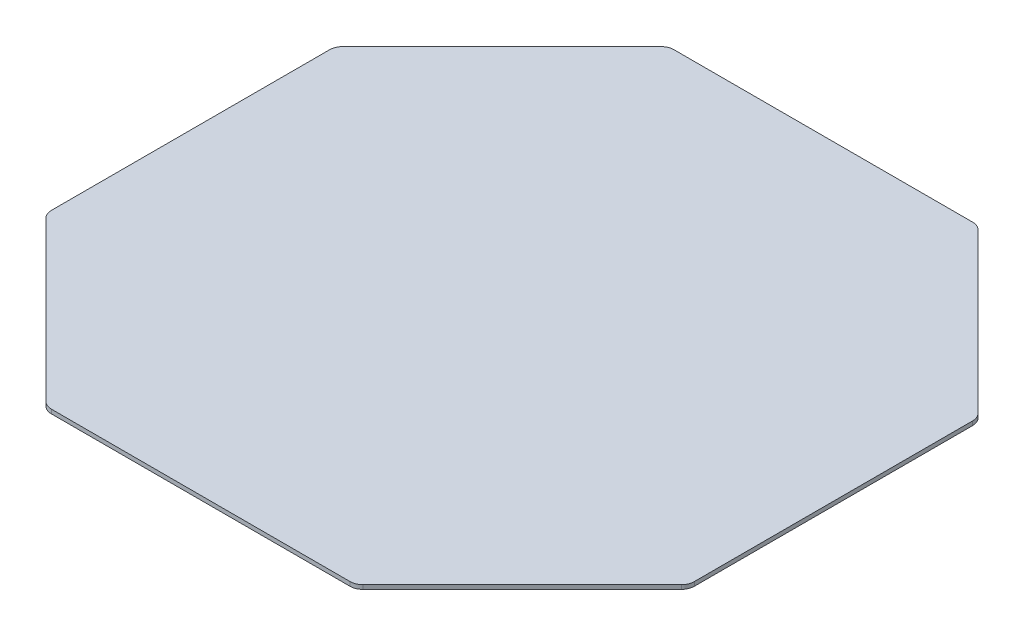
SolidWorks part; units mm, degrees
ref_plane "Front Plane" through (0, 0, 0) normal (0, 0, 1) x (1, 0, 0)
ref_plane "Top Plane" through (0, 0, 0) normal (0, 1, 0) x (1, 0, 0)
ref_plane "Right Plane" through (0, 0, 0) normal (1, 0, 0) x (0, 0, -1)
sketch "Sketch1" plane through (0, 0, 0) normal (0, 1, 0) x (1, 0, 0)
  line L0 (0, 0) -> (0, -48.0553) construction
  line L1 (25, -48.0553) -> (-25, -48.0553) construction
  line L2 (-25, -48.0553) -> (-60.3553, -12.7) construction
  line L3 (-60.3553, -12.7) -> (-60.3553, 12.7) construction
  line L4 (-60.3553, 0) -> (0, 0) construction
  line L5 (-25, 48.0553) -> (-60.3553, 12.7) construction
  line L6 (25, 48.0553) -> (-25, 48.0553) construction
  line L7 (25, 48.0553) -> (60.3553, 12.7) construction
  line L8 (60.3553, 12.7) -> (60.3553, -12.7) construction
  line L9 (25, -48.0553) -> (60.3553, -12.7) construction
  line L10 (-30.5761, 61.5173) -> (-63.5303, 28.5631)
  line L11 (-73.8173, -18.2761) -> (-73.8173, 18.2761) construction
  line L12 (-30.5761, -61.5173) -> (-63.5303, -28.5631)
  line L13 (30.5761, -61.5173) -> (-30.5761, -61.5173)
  line L14 (30.5761, -61.5173) -> (63.5303, -28.5631)
  line L15 (73.8173, 18.2761) -> (73.8173, -18.2761) construction
  line L16 (30.5761, 61.5173) -> (63.5303, 28.5631)
  line L17 (30.5761, 61.5173) -> (-30.5761, 61.5173)
  line L18 (-63.5303, 28.5631) -> (-63.5303, -28.5631)
  line L19 (-63.5303, 28.5631) -> (-73.8173, 18.2761) construction
  line L20 (-30.5761, 61.5173) -> (-73.8173, 18.2761) construction
  line L21 (-63.5303, -28.5631) -> (-73.8173, -18.2761) construction
  line L22 (-30.5761, -61.5173) -> (-73.8173, -18.2761) construction
  line L23 (63.5303, 28.5631) -> (63.5303, -28.5631)
  line L24 (63.5303, 28.5631) -> (73.8173, 18.2761) construction
  line L25 (30.5761, 61.5173) -> (73.8173, 18.2761) construction
  line L26 (63.5303, -28.5631) -> (73.8173, -18.2761) construction
  line L27 (30.5761, -61.5173) -> (73.8173, -18.2761) construction
  point P10 (0, 48.0553)
  point P23 (0, 0)
  point P25 (0, 0)
  point P27 (0, 0)
  point P29 (0, 0)
  dimension "D1" = 50
  dimension "D2" = 50
  dimension "D3" = 25.4
  dimension "D4" = 45
  dimension "D6" = 3.175
  dimension "D5" = 13.462
extrude "Extrude1" add sketch "Sketch1" along normal blind 0.8128
fillet "Fillet1" radius 2.54 8 edges at (-63.5303, 0.4064, 28.5631) (-30.5761, 0.4064, 61.5173) (-63.5303, 0.4064, -28.5631) (-30.5761, 0.4064, -61.5173) (30.5761, 0.4064, -61.5173) (63.5303, 0.4064, -28.5631) (63.5303, 0.4064, 28.5631) (30.5761, 0.4064, 61.5173)
